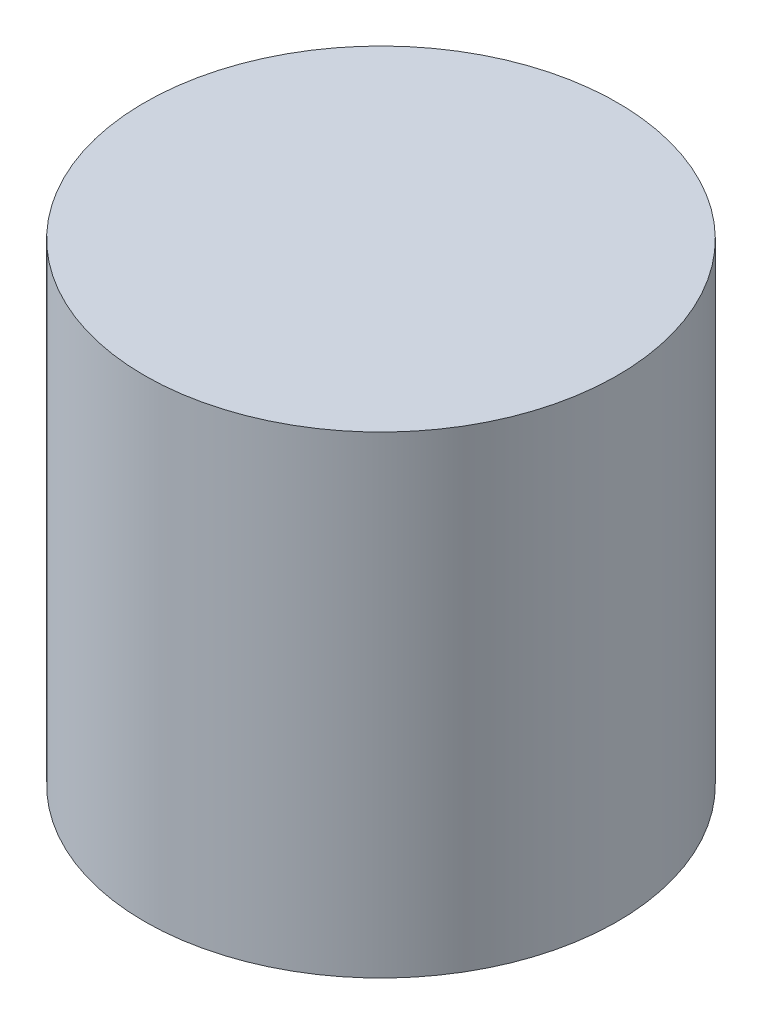
SolidWorks part; units mm, degrees
ref_plane "Front Plane" through (0, 0, 0) normal (0, 0, 1) x (1, 0, 0)
ref_plane "Top Plane" through (0, 0, 0) normal (0, 1, 0) x (1, 0, 0)
ref_plane "Right Plane" through (0, 0, 0) normal (1, 0, 0) x (0, 0, -1)
sketch "Sketch1" plane through (0, 0, 0) normal (0, 1, 0) x (1, 0, 0)
  circle A0 centre (0, 0) radius 5
  dimension "D1" = 10
extrude "Boss-Extrude1" add sketch "Sketch1" along normal blind 10
sketch "Sketch2" plane through (0, 0, 0) normal (0, -1, 0) x (1, 0, 0)
  circle A0 centre (0, 0) radius 2.5
extrude "Cut-Extrude1" cut sketch "Sketch2" against normal blind 5
sketch "Sketch3" plane through (0, 0, 0) normal (0, -1, 0) x (1, 0, 0)
  circle A0 centre (0, 0) radius 3
extrude "Cut-Extrude2" cut sketch "Sketch3" against normal blind 1.5
